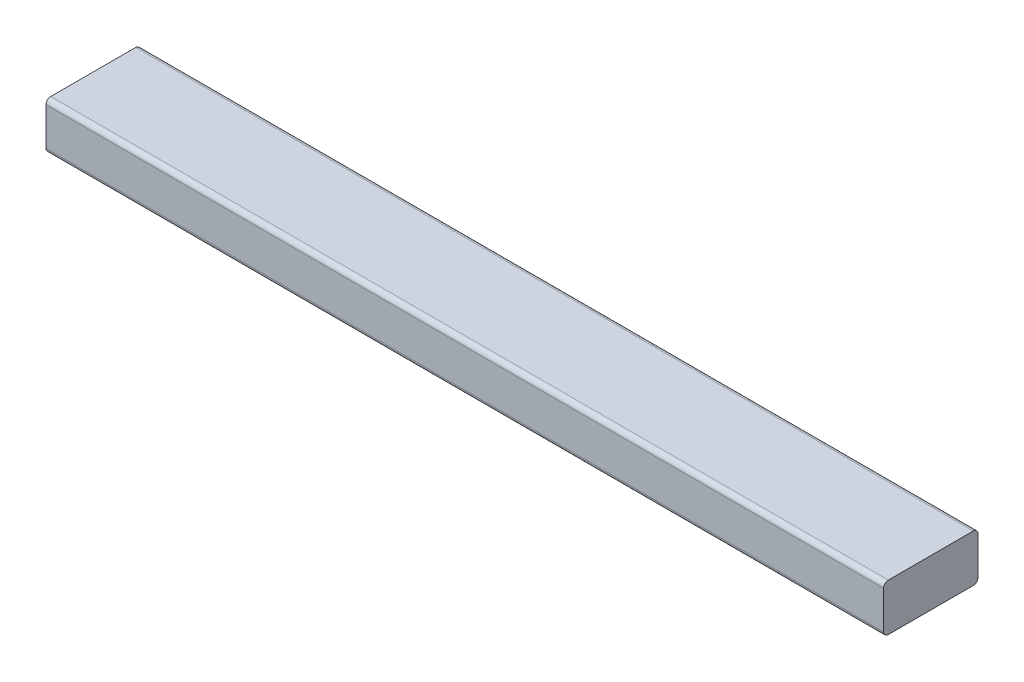
SolidWorks part; units mm, degrees
material "Balsa"
ref_plane "Front Plane" through (0, 0, 0) normal (0, 0, 1) x (1, 0, 0)
ref_plane "Top Plane" through (0, 0, 0) normal (0, 1, 0) x (1, 0, 0)
ref_plane "Right Plane" through (0, 0, 0) normal (1, 0, 0) x (0, 0, -1)
ref_plane "Plane1" through (0, -12.7, 0) normal (0, -1, 0) x (-1, 0, 0)
sketch "Sketch3" plane through (0, -12.7, 0) normal (0, -1, 0) x (-1, 0, 0)
  line L0 (-2600, -287.7) -> (-1803.322, -287.7) construction
  line L1 (-1812.7, -287.7) -> (-2714.3, -287.7)
  line L2 (-1812.7, -287.7) -> (-1812.7, -389.3)
  line L3 (-1812.7, -389.3) -> (-2714.3, -389.3)
  line L4 (-2714.3, -287.7) -> (-2714.3, -389.3)
  line L5 (-2612.7, 275) -> (-2612.7, -275) construction
  line L6 (-1812.7, -275) -> (-1812.7, -347.1543) construction
  dimension "D1" = 101.6
  dimension "D2" = 101.6
extrude "Boss-Extrude3" add sketch "Sketch3" against normal blind 50.8
fillet "Fillet1" radius 5.08 4 edges at (2263.5, 38.1, 287.7) (2263.5, -12.7, 287.7) (2263.5, -12.7, 389.3) (2263.5, 38.1, 389.3)
